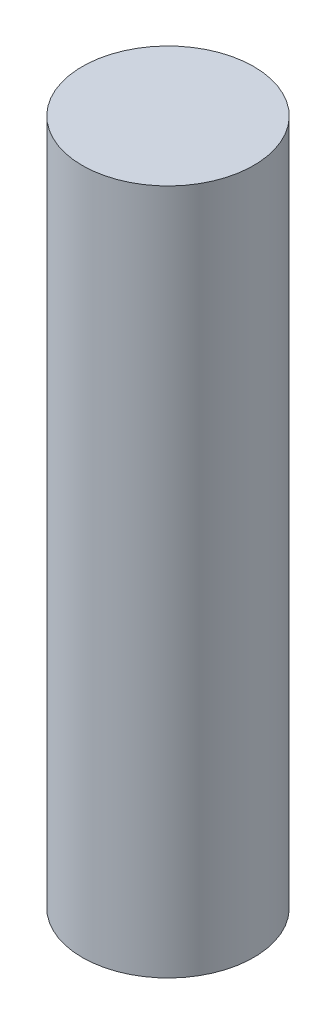
SolidWorks part; units mm, degrees
ref_plane "Front Plane" through (0, 0, 0) normal (0, 0, 1) x (1, 0, 0)
ref_plane "Top Plane" through (0, 0, 0) normal (0, 1, 0) x (1, 0, 0)
ref_plane "Right Plane" through (0, 0, 0) normal (1, 0, 0) x (0, 0, -1)
sketch "Sketch2" plane through (0, 0, 0) normal (0, 1, 0) x (1, 0, 0)
  circle A0 centre (0, 0) radius 5
  dimension "D1" = 10
extrude "Boss-Extrude1" add sketch "Sketch2" along normal blind 40
